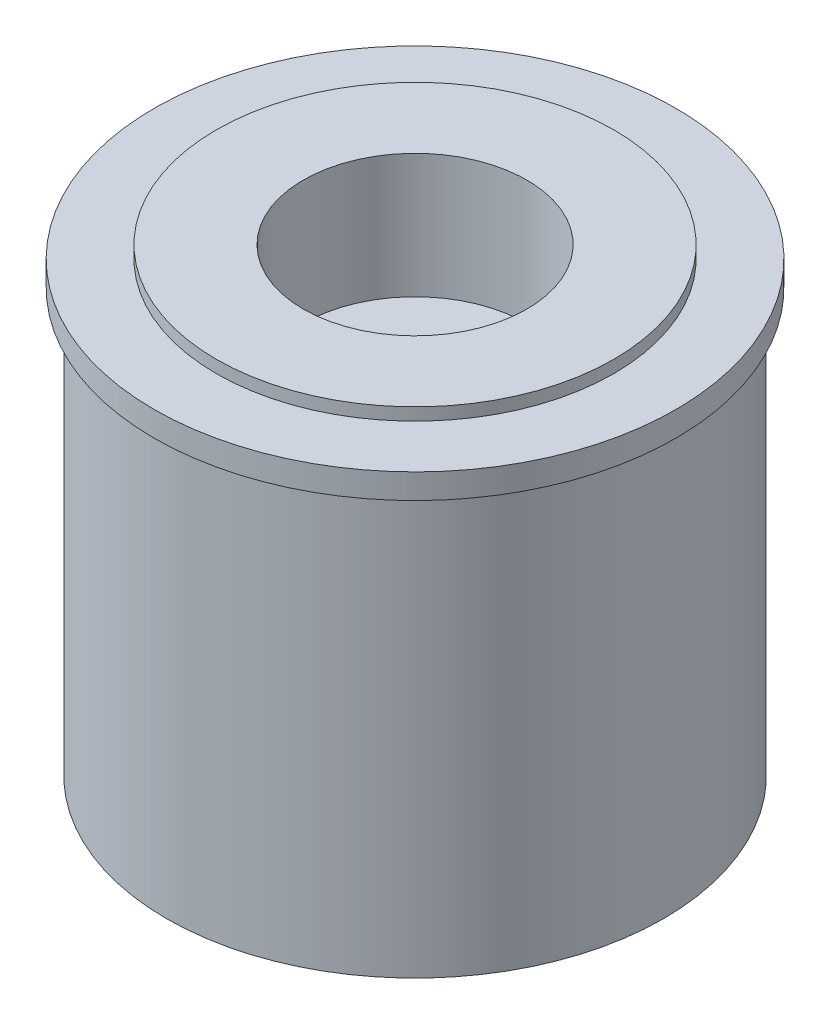
SolidWorks part; units mm, degrees
ref_plane "Frontal" through (0, 0, 0) normal (0, 0, 1) x (1, 0, 0)
ref_plane "Horizontal" through (0, 0, 0) normal (0, 1, 0) x (1, 0, 0)
ref_plane "Profile" through (0, 0, 0) normal (1, 0, 0) x (0, 0, -1)
sketch "Sketch1" plane through (0, 0, 0) normal (0, 1, 0) x (1, 0, 0)
  circle A0 centre (0, 0) radius 10
  circle A1 centre (0, 0) radius 8
extrude "Extrude1" add sketch "Sketch1" along normal blind 17
sketch "Sketch2" plane through (0, 17, 0) normal (0, 1, 0) x (-1, 0, 0)
  circle A0 centre (0, 0) radius 8
extrude "Extrude3" add sketch "Sketch2" along normal blind 10.5 from offset 9
sketch "Sketch3" plane through (0, 17, 0) normal (0, 1, 0) x (-1, 0, 0)
  circle A0 centre (0, 0) radius 10.5
extrude "Extrude4" add sketch "Sketch3" along normal blind 1
sketch "Sketch4" plane through (0, 18.5, 0) normal (0, 1, 0) x (-1, 0, 0)
  circle A0 centre (0, 0) radius 4.5
extrude "Cut-Extrude1" cut sketch "Sketch4" against normal blind 5
sketch "Sketch6" plane through (0, 8, 0) normal (0, -1, 0) x (1, 0, 0)
  circle A0 centre (6, 0) radius 2
  circle A1 centre (0, 0) radius 8 construction
extrude "Cut-Extrude4" cut sketch "Sketch6" against normal blind 5
pattern_circular "CirPattern1" count 4 over 360 about axis through (0, 0, 0) along (0, 1, 0) of "Cut-Extrude4"
sketch "Sketch7" plane through (0, 13.5, 0) normal (0, 1, 0) x (-1, 0, 0)
  line L0 (25.4553, 0) -> (-28.1918, 0) construction
  line L1 (-4.4596, -0.2) -> (-4.0596, -0.2)
  line L2 (-4.4596, -0.2) -> (-4.4596, 0.2)
  line L3 (-4.4596, 0.2) -> (-4.0596, 0.2)
  line L4 (-4.0596, -0.2) -> (-4.0596, 0.2)
  line L5 (0, -20.9577) -> (0, 19.7048) construction
  point P4 (-4.0596, 0)
  point P10 (0, 0)
extrude "Cut-Extrude5" cut sketch "Sketch7" against normal through all
pattern_circular "CirPattern2" count 4 over 360 about axis through (0, 0, 0) along (0, 1, 0) of "Cut-Extrude5"
